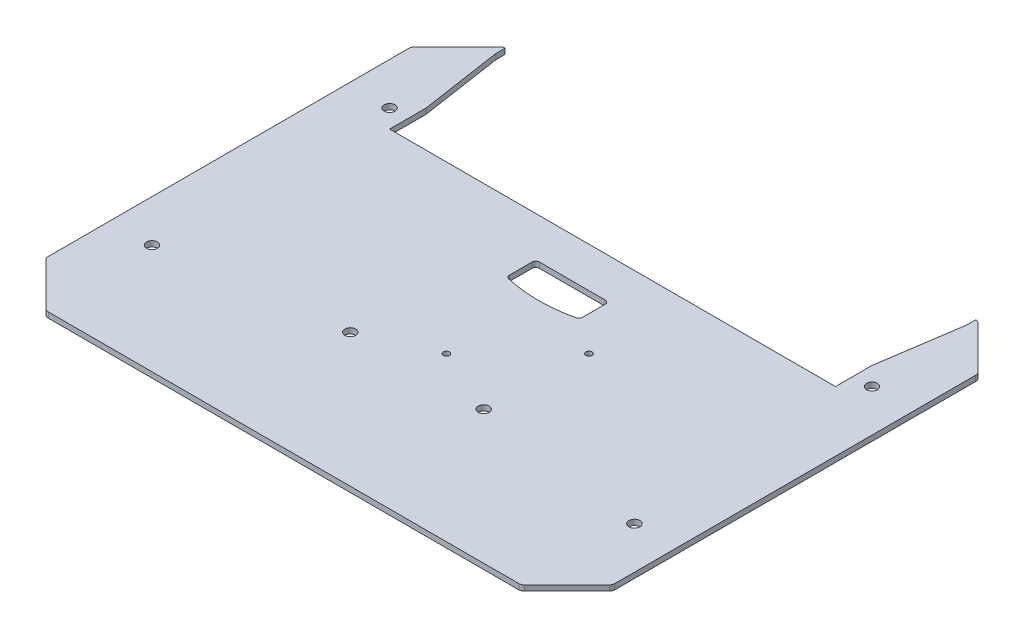
SolidWorks part; units mm, degrees
ref_plane "Plan de face" through (0, 0, 0) normal (0, 0, 1) x (1, 0, 0)
ref_plane "Plan de dessus" through (0, 0, 0) normal (0, 1, 0) x (1, 0, 0)
ref_plane "Plan de droite" through (0, 0, 0) normal (1, 0, 0) x (0, 0, -1)
sketch "Esquisse1" plane through (0, 0, 0) normal (0, 1, 0) x (1, 0, 0)
  line L0 (0, 125) -> (0, -125) construction
  line L1 (-155, 0) -> (155, 0) construction
  line L2 (-130, 125) -> (130, 125)
  line L3 (-130, -125) -> (130, -125)
  line L4 (-155, 100) -> (-155, -100)
  line L5 (155, 100) -> (155, -100)
  line L6 (-155, 100) -> (-130, 125)
  line L7 (-155, -100) -> (-130, -125)
  line L8 (130, -125) -> (155, -100)
  line L9 (130, 125) -> (155, 100)
  point P3 (0, 0)
  point P6 (0, 0)
  point P8 (0, 125)
  point P11 (0, -125)
  point P14 (-155, 0)
  point P17 (155, 0)
  dimension "D1" = 310
  dimension "D2" = 250
  dimension "D3" = 135
  dimension "D4" = 260
  dimension "D5" = 200
extrude "Boss.-Extru.1" add sketch "Esquisse1" along normal blind 3
fillet "Congé1" radius 3 8 edges at (-130, 1.5, 125) (-155, 1.5, 100) (130, 1.5, 125) (155, 1.5, 100) (155, 1.5, -100) (130, 1.5, -125) (-130, 1.5, -125) (-155, 1.5, -100)
sketch "Esquisse2" plane through (0, 3, 0) normal (0, 1, 0) x (1, 0, 0)
  line L0 (0, 125) -> (0, -125) construction
  line L1 (128.7574, 125) -> (-128.7574, 125) construction
  line L2 (-128.7574, -125) -> (128.7574, -125) construction
  line L3 (-155, 0) -> (155, 0) construction
  line L4 (-155, 98.7574) -> (-155, -98.7574) construction
  line L5 (155, -98.7574) -> (155, 98.7574) construction
  line L6 (-132, 65) -> (-132, 0) construction
  line L7 (-132, 65) -> (-155, 65) construction
  circle A0 centre (-132, 65) radius 3
  circle A1 centre (-132, -65) radius 3
  circle A2 centre (132, -65) radius 3
  circle A3 centre (132, 65) radius 3
  dimension "D1" = 6
  dimension "D2" = 23
  dimension "D3" = 65
extrude "Perçage Profilé" cut sketch "Esquisse2" against normal through all
sketch "Esquisse3" plane through (0, 3, 0) normal (0, 1, 0) x (1, 0, 0)
  line L0 (0, -125) -> (0, -52) construction
  line L1 (-128.7574, -125) -> (128.7574, -125) construction
  line L2 (-36.5, -52) -> (36.5, -52) construction
  circle A0 centre (-36.5, -52) radius 3
  circle A1 centre (36.5, -52) radius 3
  point P8 (0, -52)
  dimension "D1" = 6
  dimension "D2" = 73
  dimension "D3" = 73
extrude "Enlèv. mat.-Extru.1" cut sketch "Esquisse3" against normal through all
sketch "Esquisse5" plane through (0, 3, 0) normal (0, 1, 0) x (1, 0, 0)
  line L0 (0, 0) -> (0, 3.11) construction
  line L1 (0, 3.11) -> (0, -35.89) construction
  line L2 (0, 3.11) -> (39, 3.11) construction
  circle A0 centre (0, -35.89) radius 1.7
  circle A1 centre (39, 3.11) radius 1.7
  point P7 (0, 19.7894)
  dimension "D1" = 3.11
  dimension "D3" = 3.4
  dimension "D2" = 39
extrude "Enlèv. mat.-Extru.3" cut sketch "Esquisse5" against normal up to next
sketch "Esquisse6" plane through (0, 3, 0) normal (0, 1, 0) x (1, 0, 0)
  line L0 (0, 33) -> (0, 0) construction
  line L1 (-20, 33) -> (20, 33)
  line L2 (-20, 33) -> (-20, 17)
  line L3 (-20, 17) -> (20, 17) construction
  line L4 (20, 33) -> (20, 17)
  arc A0 (-20, 17) -> (20, 17) centre (0, 96.5236) ccw
  point P8 (0, 69.9474)
  dimension "D3" = 82
  dimension "D1" = 16
  dimension "D2" = 40
  dimension "D4" = 33
extrude "Enlèv. mat.-Extru.4" cut sketch "Esquisse6" against normal up to next
fillet "Congé2" radius 2 4 edges at (-20, 1.5, -17) (-20, 1.5, -33) (20, 1.5, -33) (20, 1.5, -17)
sketch "Esquisse4" plane through (0, 3, 0) normal (0, 1, 0) x (1, 0, 0)
  line L0 (122, 55) -> (-122, 55)
  line L1 (-122, 55) -> (-122, 75)
  line L3 (-128.7574, 125) -> (128.7574, 125)
  line L5 (122, 75) -> (122, 55)
  line L6 (155, -98.7574) -> (155, 98.7574) construction
  line L7 (0, 55) -> (0, 125) construction
  line L8 (128.7574, 125) -> (128.7574, 120)
  line L9 (128.7574, 120) -> (122, 75)
  line L10 (-128.7574, 125) -> (-128.7574, 120)
  line L11 (-128.7574, 120) -> (-122, 75)
  dimension "D1" = 33
  dimension "D2" = 70
  dimension "D3" = 20
  dimension "D4" = 5
extrude "Enlèv. mat.-Extru.2" cut sketch "Esquisse4" against normal up to next
